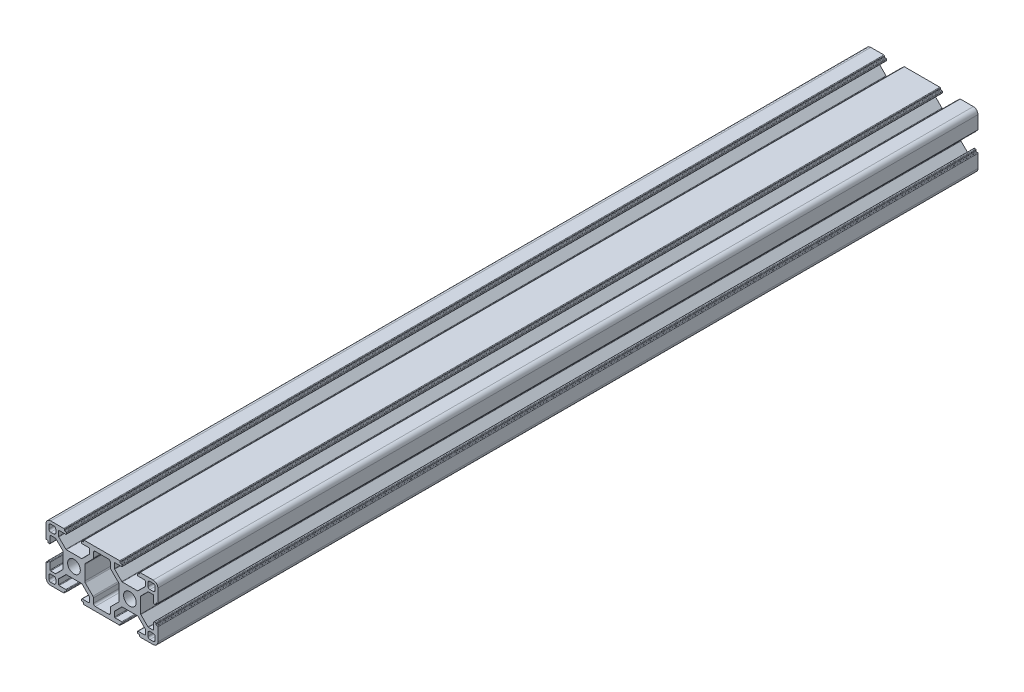
SolidWorks part; units mm, degrees
ref_plane "前视基准面" through (0, 0, 0) normal (0, 0, 1) x (1, 0, 0)
ref_plane "上视基准面" through (0, 0, 0) normal (0, 1, 0) x (1, 0, 0)
ref_plane "右视基准面" through (0, 0, 0) normal (1, 0, 0) x (0, 0, -1)
sketch "Model" plane through (0, 0, 0) normal (0, 0, 1) x (1, 0, 0)
  line L0 (154.3439, 58.7492) -> (156.0939, 58.7492)
  line L1 (157.0939, 57.7492) -> (157.0939, 55.9992)
  line L2 (156.0939, 54.9992) -> (154.3439, 54.9992)
  line L3 (153.3439, 55.9992) -> (153.3439, 57.7492)
  line L4 (102.8439, 58.7492) -> (101.0939, 58.7492)
  line L5 (100.0939, 57.7492) -> (100.0939, 55.9992)
  line L6 (101.0939, 54.9992) -> (102.8439, 54.9992)
  line L7 (103.8439, 55.9992) -> (103.8439, 57.7492)
  line L8 (147.9939, 59.2492) -> (148.4939, 59.2492)
  line L9 (148.7939, 59.5492) -> (148.7939, 59.9492)
  line L10 (149.0939, 60.2492) -> (156.0939, 60.2492)
  line L11 (158.5939, 57.7492) -> (158.5939, 50.7492)
  line L12 (158.2939, 50.4492) -> (157.8939, 50.4492)
  line L13 (157.5939, 50.1492) -> (157.5939, 49.6492)
  line L14 (157.2939, 49.3492) -> (156.6939, 49.3492)
  line L15 (156.3939, 49.6492) -> (156.3939, 53.1992)
  line L16 (156.0939, 53.4992) -> (153.5238, 53.4992)
  line L17 (153.3117, 53.4113) -> (149.4818, 49.5814)
  line L18 (149.3939, 49.3693) -> (149.3939, 45.2492)
  line L19 (149.3939, 45.2492) -> (149.3939, 41.1291)
  line L20 (149.4818, 40.9169) -> (153.3117, 37.087)
  line L21 (153.5238, 36.9992) -> (156.0939, 36.9992)
  line L22 (156.3939, 37.2992) -> (156.3939, 40.8492)
  line L23 (156.6939, 41.1492) -> (157.2939, 41.1492)
  line L24 (157.5939, 40.8492) -> (157.5939, 40.3492)
  line L25 (157.8939, 40.0492) -> (158.2939, 40.0492)
  line L26 (158.5939, 39.7492) -> (158.5939, 32.7492)
  line L27 (156.0939, 30.2492) -> (149.0939, 30.2492)
  line L28 (148.7939, 30.5492) -> (148.7939, 30.9492)
  line L29 (148.4939, 31.2492) -> (147.9939, 31.2492)
  line L30 (147.6939, 31.5492) -> (147.6939, 32.1492)
  line L31 (147.9939, 32.4492) -> (151.5439, 32.4492)
  line L32 (151.8439, 32.7492) -> (151.8439, 35.3193)
  line L33 (151.756, 35.5314) -> (147.9261, 39.3613)
  line L34 (147.714, 39.4492) -> (143.5939, 39.4492)
  line L35 (143.5939, 39.4492) -> (139.4738, 39.4492)
  line L36 (139.2617, 39.3613) -> (135.4318, 35.5314)
  line L37 (135.3439, 35.3193) -> (135.3439, 32.7492)
  line L38 (135.6439, 32.4492) -> (139.1939, 32.4492)
  line L39 (139.4939, 32.1492) -> (139.4939, 31.5492)
  line L40 (139.1939, 31.2492) -> (138.6939, 31.2492)
  line L41 (138.3939, 30.9492) -> (138.3939, 30.5492)
  line L42 (138.0939, 30.2492) -> (119.0939, 30.2492)
  line L43 (118.7939, 30.5492) -> (118.7939, 30.9492)
  line L44 (118.4939, 31.2492) -> (117.9939, 31.2492)
  line L45 (117.6939, 31.5492) -> (117.6939, 32.1492)
  line L46 (117.9939, 32.4492) -> (121.5439, 32.4492)
  line L47 (121.8439, 32.7492) -> (121.8439, 35.3193)
  line L48 (121.756, 35.5314) -> (117.9261, 39.3613)
  line L49 (117.714, 39.4492) -> (113.5939, 39.4492)
  line L50 (113.5939, 39.4492) -> (109.4738, 39.4492)
  line L51 (109.2617, 39.3613) -> (105.4318, 35.5314)
  line L52 (105.3439, 35.3193) -> (105.3439, 32.7492)
  line L53 (105.6439, 32.4492) -> (109.1939, 32.4492)
  line L54 (109.4939, 32.1492) -> (109.4939, 31.5492)
  line L55 (109.1939, 31.2492) -> (108.6939, 31.2492)
  line L56 (108.3939, 30.9492) -> (108.3939, 30.5492)
  line L57 (108.0939, 30.2492) -> (101.0939, 30.2492)
  line L58 (98.5939, 32.7492) -> (98.5939, 39.7492)
  line L59 (98.8939, 40.0492) -> (99.2939, 40.0492)
  line L60 (99.5939, 40.3492) -> (99.5939, 40.8492)
  line L61 (99.8939, 41.1492) -> (100.4939, 41.1492)
  line L62 (100.7939, 40.8492) -> (100.7939, 37.2992)
  line L63 (101.0939, 36.9992) -> (103.664, 36.9992)
  line L64 (103.8761, 37.087) -> (107.706, 40.9169)
  line L65 (107.7939, 41.1291) -> (107.7939, 45.2492)
  line L66 (107.7939, 45.2492) -> (107.7939, 49.3693)
  line L67 (107.706, 49.5814) -> (103.8761, 53.4113)
  line L68 (103.664, 53.4992) -> (101.0939, 53.4992)
  line L69 (100.7939, 53.1992) -> (100.7939, 49.6492)
  line L70 (100.4939, 49.3492) -> (99.8939, 49.3492)
  line L71 (99.5939, 49.6492) -> (99.5939, 50.1492)
  line L72 (99.2939, 50.4492) -> (98.8939, 50.4492)
  line L73 (98.5939, 50.7492) -> (98.5939, 57.7492)
  line L74 (101.0939, 60.2492) -> (108.0939, 60.2492)
  line L75 (108.3939, 59.9492) -> (108.3939, 59.5492)
  line L76 (108.6939, 59.2492) -> (109.1939, 59.2492)
  line L77 (109.4939, 58.9492) -> (109.4939, 58.3492)
  line L78 (109.1939, 58.0492) -> (105.6439, 58.0492)
  line L79 (105.3439, 57.7492) -> (105.3439, 55.1791)
  line L80 (105.4318, 54.9669) -> (109.2617, 51.137)
  line L81 (109.4738, 51.0492) -> (113.5939, 51.0492)
  line L82 (113.5939, 51.0492) -> (117.714, 51.0492)
  line L83 (117.9261, 51.137) -> (121.756, 54.9669)
  line L84 (121.8439, 55.1791) -> (121.8439, 57.7492)
  line L85 (121.5439, 58.0492) -> (117.9939, 58.0492)
  line L86 (117.6939, 58.3492) -> (117.6939, 58.9492)
  line L87 (117.9939, 59.2492) -> (118.4939, 59.2492)
  line L88 (118.7939, 59.5492) -> (118.7939, 59.9492)
  line L89 (119.0939, 60.2492) -> (138.0939, 60.2492)
  line L90 (138.3939, 59.9492) -> (138.3939, 59.5492)
  line L91 (138.6939, 59.2492) -> (139.1939, 59.2492)
  line L92 (139.4939, 58.9492) -> (139.4939, 58.3492)
  line L93 (139.1939, 58.0492) -> (135.6439, 58.0492)
  line L94 (135.3439, 57.7492) -> (135.3439, 55.1791)
  line L95 (135.4318, 54.9669) -> (139.2617, 51.137)
  line L96 (139.4738, 51.0492) -> (143.5939, 51.0492)
  line L97 (143.5939, 51.0492) -> (147.714, 51.0492)
  line L98 (147.9261, 51.137) -> (151.756, 54.9669)
  line L99 (151.8439, 55.1791) -> (151.8439, 57.7492)
  line L100 (151.5439, 58.0492) -> (147.9939, 58.0492)
  line L101 (147.6939, 58.3492) -> (147.6939, 58.9492)
  line L103 (154.3439, 31.7492) -> (156.0939, 31.7492)
  line L104 (157.0939, 32.7492) -> (157.0939, 34.4992)
  line L105 (156.0939, 35.4992) -> (154.3439, 35.4992)
  line L106 (153.3439, 34.4992) -> (153.3439, 32.7492)
  line L108 (119.3939, 49.0793) -> (119.3939, 45.2492)
  line L109 (119.3939, 45.2492) -> (119.3939, 41.419)
  line L110 (119.6868, 40.7119) -> (123.751, 36.6477)
  line L111 (124.0439, 35.9406) -> (124.0439, 33.4492)
  line L112 (125.0439, 32.4492) -> (128.5939, 32.4492)
  line L113 (128.5939, 32.4492) -> (132.1439, 32.4492)
  line L114 (133.1439, 33.4492) -> (133.1439, 35.9406)
  line L115 (133.4368, 36.6477) -> (137.501, 40.7119)
  line L116 (137.7939, 41.419) -> (137.7939, 45.2492)
  line L117 (137.7939, 45.2492) -> (137.7939, 49.0793)
  line L118 (137.501, 49.7864) -> (133.4368, 53.8507)
  line L119 (133.1439, 54.5578) -> (133.1439, 57.0492)
  line L120 (132.1439, 58.0492) -> (128.5939, 58.0492)
  line L121 (128.5939, 58.0492) -> (125.0439, 58.0492)
  line L122 (124.0439, 57.0492) -> (124.0439, 54.5578)
  line L123 (123.751, 53.8507) -> (119.6868, 49.7864)
  line L128 (102.8439, 31.7492) -> (101.0939, 31.7492)
  line L129 (100.0939, 32.7492) -> (100.0939, 34.4992)
  line L130 (101.0939, 35.4992) -> (102.8439, 35.4992)
  line L131 (103.8439, 34.4992) -> (103.8439, 32.7492)
  circle A0 centre (113.5939, 45.2492) radius 3.4
  circle A1 centre (143.5939, 45.2492) radius 3.4
  arc A2 (154.3439, 58.7492) -> (153.3439, 57.7492) centre (154.3439, 57.7492) ccw
  arc A3 (157.0939, 57.7492) -> (156.0939, 58.7492) centre (156.0939, 57.7492) ccw
  arc A4 (156.0939, 54.9992) -> (157.0939, 55.9992) centre (156.0939, 55.9992) ccw
  arc A5 (153.3439, 55.9992) -> (154.3439, 54.9992) centre (154.3439, 55.9992) ccw
  arc A6 (103.8439, 57.7492) -> (102.8439, 58.7492) centre (102.8439, 57.7492) ccw
  arc A7 (101.0939, 58.7492) -> (100.0939, 57.7492) centre (101.0939, 57.7492) ccw
  arc A8 (100.0939, 55.9992) -> (101.0939, 54.9992) centre (101.0939, 55.9992) ccw
  arc A9 (102.8439, 54.9992) -> (103.8439, 55.9992) centre (102.8439, 55.9992) ccw
  arc A10 (148.4939, 59.2492) -> (148.7939, 59.5492) centre (148.4939, 59.5492) ccw
  arc A11 (149.0939, 60.2492) -> (148.7939, 59.9492) centre (149.0939, 59.9492) ccw
  arc A12 (158.5939, 57.7492) -> (156.0939, 60.2492) centre (156.0939, 57.7492) ccw
  arc A13 (158.2939, 50.4492) -> (158.5939, 50.7492) centre (158.2939, 50.7492) ccw
  arc A14 (157.8939, 50.4492) -> (157.5939, 50.1492) centre (157.8939, 50.1492) ccw
  arc A15 (157.2939, 49.3492) -> (157.5939, 49.6492) centre (157.2939, 49.6492) ccw
  arc A16 (156.3939, 49.6492) -> (156.6939, 49.3492) centre (156.6939, 49.6492) ccw
  arc A17 (156.3939, 53.1992) -> (156.0939, 53.4992) centre (156.0939, 53.1992) ccw
  arc A18 (153.5238, 53.4992) -> (153.3117, 53.4113) centre (153.5238, 53.1992) ccw
  arc A19 (149.4818, 49.5814) -> (149.3939, 49.3693) centre (149.6939, 49.3693) ccw
  arc A20 (149.3939, 41.1291) -> (149.4818, 40.9169) centre (149.6939, 41.1291) ccw
  arc A21 (153.3117, 37.087) -> (153.5238, 36.9992) centre (153.5238, 37.2992) ccw
  arc A22 (156.0939, 36.9992) -> (156.3939, 37.2992) centre (156.0939, 37.2992) ccw
  arc A23 (156.6939, 41.1492) -> (156.3939, 40.8492) centre (156.6939, 40.8492) ccw
  arc A24 (157.5939, 40.8492) -> (157.2939, 41.1492) centre (157.2939, 40.8492) ccw
  arc A25 (157.5939, 40.3492) -> (157.8939, 40.0492) centre (157.8939, 40.3492) ccw
  arc A26 (158.5939, 39.7492) -> (158.2939, 40.0492) centre (158.2939, 39.7492) ccw
  arc A27 (156.0939, 30.2492) -> (158.5939, 32.7492) centre (156.0939, 32.7492) ccw
  arc A28 (148.7939, 30.5492) -> (149.0939, 30.2492) centre (149.0939, 30.5492) ccw
  arc A29 (148.7939, 30.9492) -> (148.4939, 31.2492) centre (148.4939, 30.9492) ccw
  arc A30 (147.6939, 31.5492) -> (147.9939, 31.2492) centre (147.9939, 31.5492) ccw
  arc A31 (147.9939, 32.4492) -> (147.6939, 32.1492) centre (147.9939, 32.1492) ccw
  arc A32 (151.5439, 32.4492) -> (151.8439, 32.7492) centre (151.5439, 32.7492) ccw
  arc A33 (151.8439, 35.3193) -> (151.756, 35.5314) centre (151.5439, 35.3193) ccw
  arc A34 (147.9261, 39.3613) -> (147.714, 39.4492) centre (147.714, 39.1492) ccw
  arc A35 (139.4738, 39.4492) -> (139.2617, 39.3613) centre (139.4738, 39.1492) ccw
  arc A36 (135.4318, 35.5314) -> (135.3439, 35.3193) centre (135.6439, 35.3193) ccw
  arc A37 (135.3439, 32.7492) -> (135.6439, 32.4492) centre (135.6439, 32.7492) ccw
  arc A38 (139.4939, 32.1492) -> (139.1939, 32.4492) centre (139.1939, 32.1492) ccw
  arc A39 (139.1939, 31.2492) -> (139.4939, 31.5492) centre (139.1939, 31.5492) ccw
  arc A40 (138.6939, 31.2492) -> (138.3939, 30.9492) centre (138.6939, 30.9492) ccw
  arc A41 (138.0939, 30.2492) -> (138.3939, 30.5492) centre (138.0939, 30.5492) ccw
  arc A42 (118.7939, 30.5492) -> (119.0939, 30.2492) centre (119.0939, 30.5492) ccw
  arc A43 (118.7939, 30.9492) -> (118.4939, 31.2492) centre (118.4939, 30.9492) ccw
  arc A44 (117.6939, 31.5492) -> (117.9939, 31.2492) centre (117.9939, 31.5492) ccw
  arc A45 (117.9939, 32.4492) -> (117.6939, 32.1492) centre (117.9939, 32.1492) ccw
  arc A46 (121.5439, 32.4492) -> (121.8439, 32.7492) centre (121.5439, 32.7492) ccw
  arc A47 (121.8439, 35.3193) -> (121.756, 35.5314) centre (121.5439, 35.3193) ccw
  arc A48 (117.9261, 39.3613) -> (117.714, 39.4492) centre (117.714, 39.1492) ccw
  arc A49 (109.4738, 39.4492) -> (109.2617, 39.3613) centre (109.4738, 39.1492) ccw
  arc A50 (105.4318, 35.5314) -> (105.3439, 35.3193) centre (105.6439, 35.3193) ccw
  arc A51 (105.3439, 32.7492) -> (105.6439, 32.4492) centre (105.6439, 32.7492) ccw
  arc A52 (109.4939, 32.1492) -> (109.1939, 32.4492) centre (109.1939, 32.1492) ccw
  arc A53 (109.1939, 31.2492) -> (109.4939, 31.5492) centre (109.1939, 31.5492) ccw
  arc A54 (108.6939, 31.2492) -> (108.3939, 30.9492) centre (108.6939, 30.9492) ccw
  arc A55 (108.0939, 30.2492) -> (108.3939, 30.5492) centre (108.0939, 30.5492) ccw
  arc A56 (98.5939, 32.7492) -> (101.0939, 30.2492) centre (101.0939, 32.7492) ccw
  arc A57 (98.8939, 40.0492) -> (98.5939, 39.7492) centre (98.8939, 39.7492) ccw
  arc A58 (99.2939, 40.0492) -> (99.5939, 40.3492) centre (99.2939, 40.3492) ccw
  arc A59 (99.8939, 41.1492) -> (99.5939, 40.8492) centre (99.8939, 40.8492) ccw
  arc A60 (100.7939, 40.8492) -> (100.4939, 41.1492) centre (100.4939, 40.8492) ccw
  arc A61 (100.7939, 37.2992) -> (101.0939, 36.9992) centre (101.0939, 37.2992) ccw
  arc A62 (103.664, 36.9992) -> (103.8761, 37.087) centre (103.664, 37.2992) ccw
  arc A63 (107.706, 40.9169) -> (107.7939, 41.1291) centre (107.4939, 41.1291) ccw
  arc A64 (107.7939, 49.3693) -> (107.706, 49.5814) centre (107.4939, 49.3693) ccw
  arc A65 (103.8761, 53.4113) -> (103.664, 53.4992) centre (103.664, 53.1992) ccw
  arc A66 (101.0939, 53.4992) -> (100.7939, 53.1992) centre (101.0939, 53.1992) ccw
  arc A67 (100.4939, 49.3492) -> (100.7939, 49.6492) centre (100.4939, 49.6492) ccw
  arc A68 (99.5939, 49.6492) -> (99.8939, 49.3492) centre (99.8939, 49.6492) ccw
  arc A69 (99.5939, 50.1492) -> (99.2939, 50.4492) centre (99.2939, 50.1492) ccw
  arc A70 (98.5939, 50.7492) -> (98.8939, 50.4492) centre (98.8939, 50.7492) ccw
  arc A71 (101.0939, 60.2492) -> (98.5939, 57.7492) centre (101.0939, 57.7492) ccw
  arc A72 (108.3939, 59.9492) -> (108.0939, 60.2492) centre (108.0939, 59.9492) ccw
  arc A73 (108.3939, 59.5492) -> (108.6939, 59.2492) centre (108.6939, 59.5492) ccw
  arc A74 (109.4939, 58.9492) -> (109.1939, 59.2492) centre (109.1939, 58.9492) ccw
  arc A75 (109.1939, 58.0492) -> (109.4939, 58.3492) centre (109.1939, 58.3492) ccw
  arc A76 (105.6439, 58.0492) -> (105.3439, 57.7492) centre (105.6439, 57.7492) ccw
  arc A77 (105.3439, 55.1791) -> (105.4318, 54.9669) centre (105.6439, 55.1791) ccw
  arc A78 (109.2617, 51.137) -> (109.4738, 51.0492) centre (109.4738, 51.3492) ccw
  arc A79 (117.714, 51.0492) -> (117.9261, 51.137) centre (117.714, 51.3492) ccw
  arc A80 (121.756, 54.9669) -> (121.8439, 55.1791) centre (121.5439, 55.1791) ccw
  arc A81 (121.8439, 57.7492) -> (121.5439, 58.0492) centre (121.5439, 57.7492) ccw
  arc A82 (117.6939, 58.3492) -> (117.9939, 58.0492) centre (117.9939, 58.3492) ccw
  arc A83 (117.9939, 59.2492) -> (117.6939, 58.9492) centre (117.9939, 58.9492) ccw
  arc A84 (118.4939, 59.2492) -> (118.7939, 59.5492) centre (118.4939, 59.5492) ccw
  arc A85 (119.0939, 60.2492) -> (118.7939, 59.9492) centre (119.0939, 59.9492) ccw
  arc A86 (138.3939, 59.9492) -> (138.0939, 60.2492) centre (138.0939, 59.9492) ccw
  arc A87 (138.3939, 59.5492) -> (138.6939, 59.2492) centre (138.6939, 59.5492) ccw
  arc A88 (139.4939, 58.9492) -> (139.1939, 59.2492) centre (139.1939, 58.9492) ccw
  arc A89 (139.1939, 58.0492) -> (139.4939, 58.3492) centre (139.1939, 58.3492) ccw
  arc A90 (135.6439, 58.0492) -> (135.3439, 57.7492) centre (135.6439, 57.7492) ccw
  arc A91 (135.3439, 55.1791) -> (135.4318, 54.9669) centre (135.6439, 55.1791) ccw
  arc A92 (139.2617, 51.137) -> (139.4738, 51.0492) centre (139.4738, 51.3492) ccw
  arc A93 (147.714, 51.0492) -> (147.9261, 51.137) centre (147.714, 51.3492) ccw
  arc A94 (151.756, 54.9669) -> (151.8439, 55.1791) centre (151.5439, 55.1791) ccw
  arc A95 (151.8439, 57.7492) -> (151.5439, 58.0492) centre (151.5439, 57.7492) ccw
  arc A96 (147.6939, 58.3492) -> (147.9939, 58.0492) centre (147.9939, 58.3492) ccw
  arc A97 (147.9939, 59.2492) -> (147.6939, 58.9492) centre (147.9939, 58.9492) ccw
  arc A98 (153.3439, 32.7492) -> (154.3439, 31.7492) centre (154.3439, 32.7492) ccw
  arc A99 (156.0939, 31.7492) -> (157.0939, 32.7492) centre (156.0939, 32.7492) ccw
  arc A100 (157.0939, 34.4992) -> (156.0939, 35.4992) centre (156.0939, 34.4992) ccw
  arc A101 (154.3439, 35.4992) -> (153.3439, 34.4992) centre (154.3439, 34.4992) ccw
  arc A102 (119.6868, 49.7864) -> (119.3939, 49.0793) centre (120.3939, 49.0793) ccw
  arc A103 (119.3939, 41.419) -> (119.6868, 40.7119) centre (120.3939, 41.419) ccw
  arc A104 (124.0439, 35.9406) -> (123.751, 36.6477) centre (123.0439, 35.9406) ccw
  arc A105 (124.0439, 33.4492) -> (125.0439, 32.4492) centre (125.0439, 33.4492) ccw
  arc A106 (132.1439, 32.4492) -> (133.1439, 33.4492) centre (132.1439, 33.4492) ccw
  arc A107 (133.4368, 36.6477) -> (133.1439, 35.9406) centre (134.1439, 35.9406) ccw
  arc A108 (137.501, 40.7119) -> (137.7939, 41.419) centre (136.7939, 41.419) ccw
  arc A109 (137.7939, 49.0793) -> (137.501, 49.7864) centre (136.7939, 49.0793) ccw
  arc A110 (133.1439, 54.5578) -> (133.4368, 53.8507) centre (134.1439, 54.5578) ccw
  arc A111 (133.1439, 57.0492) -> (132.1439, 58.0492) centre (132.1439, 57.0492) ccw
  arc A112 (125.0439, 58.0492) -> (124.0439, 57.0492) centre (125.0439, 57.0492) ccw
  arc A113 (123.751, 53.8507) -> (124.0439, 54.5578) centre (123.0439, 54.5578) ccw
  arc A114 (102.8439, 31.7492) -> (103.8439, 32.7492) centre (102.8439, 32.7492) ccw
  arc A115 (100.0939, 32.7492) -> (101.0939, 31.7492) centre (101.0939, 32.7492) ccw
  arc A116 (101.0939, 35.4992) -> (100.0939, 34.4992) centre (101.0939, 34.4992) ccw
  arc A117 (103.8439, 34.4992) -> (102.8439, 35.4992) centre (102.8439, 34.4992) ccw
extrude "凸台-拉伸1" add sketch "Model" along normal blind 440
